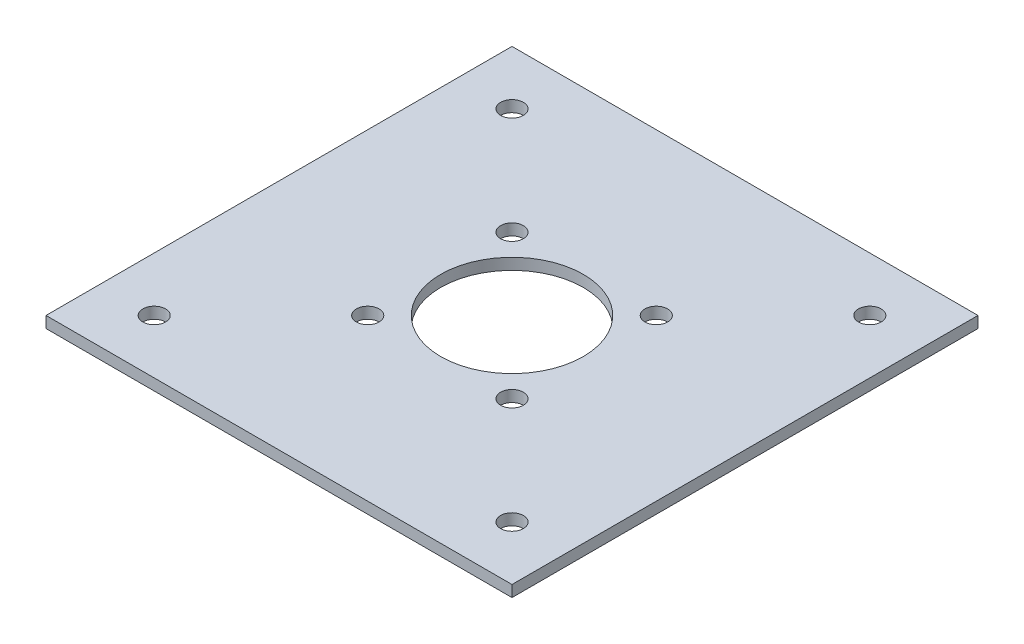
SolidWorks part; units mm, degrees
material "201 Annealed Stainless Steel (SS)"
ref_plane "Front Plane" through (0, 0, 0) normal (0, 0, 1) x (1, 0, 0)
ref_plane "Top Plane" through (0, 0, 0) normal (0, 1, 0) x (1, 0, 0)
ref_plane "Right Plane" through (0, 0, 0) normal (1, 0, 0) x (0, 0, -1)
sketch "Sketch1" plane through (0, 0, 0) normal (0, 1, 0) x (1, 0, 0)
  line L1 (0, 0) -> (82.042, 0)
  line L2 (0, 0) -> (0, 82.042)
  line L3 (0, 82.042) -> (82.042, 82.042)
  line L4 (82.042, 0) -> (82.042, 82.042)
  dimension "D1" = 82.042
  dimension "D2" = 82.042
extrude "Boss-Extrude1" add sketch "Sketch1" along normal blind 2
sketch "Sketch2" plane through (0, 2, 0) normal (0, 1, 0) x (-1, 0, 0)
  line L0 (-41.021, -82.042) -> (-41.021, 0) construction
  line L1 (-82.042, -82.042) -> (0, -82.042) construction
  line L2 (0, 0) -> (-82.042, 0) construction
  line L3 (0, -41.021) -> (-82.042, -41.021) construction
  line L4 (0, -82.042) -> (0, 0) construction
  line L5 (-82.042, 0) -> (-82.042, -82.042) construction
  line L6 (-28.321, -82.042) -> (-28.321, 0)
  line L7 (-53.721, -82.042) -> (-53.721, 0)
  line L8 (-82.042, 0) -> (-82.042, -82.042) construction
  line L9 (-72.517, 0) -> (-72.517, -82.042)
  line L10 (-9.525, 0) -> (-9.525, -82.042)
  line L11 (0, -82.042) -> (-82.042, -82.042) construction
  line L12 (0, -28.321) -> (-82.042, -28.321)
  line L13 (0, -53.721) -> (-82.042, -53.721)
  line L15 (-82.042, -9.525) -> (0, -9.525)
  line L16 (-82.042, -72.517) -> (0, -72.517)
  line L17 (-82.042, -72.517) -> (0, -72.517)
  circle A0 centre (-28.321, -53.721) radius 2
  circle A1 centre (-53.721, -53.721) radius 2
  circle A2 centre (-53.721, -28.321) radius 2
  circle A3 centre (-28.321, -28.321) radius 2
  circle A4 centre (-9.525, -9.525) radius 2
  circle A5 centre (-9.525, -72.517) radius 2
  circle A6 centre (-72.517, -9.525) radius 2
  circle A7 centre (-72.517, -72.517) radius 2
  circle A8 centre (-41.021, -41.021) radius 12.6746
  dimension "D5" = 9.525
  dimension "D1" = 12.7
  dimension "D2" = 12.7
  dimension "D3" = 12.7
  dimension "D4" = 12.7
  dimension "D6" = 9.525
extrude "Cut-Extrude1" cut sketch "Sketch2" against normal through all contours A5 | A0 | A3 | A2 | A1 | A7 | A6 | A4
sketch "Sketch3" plane through (0, 2, 0) normal (0, 1, 0) x (1, 0, 0)
  line L0 (0, 41.021) -> (82.042, 41.021) construction
  line L1 (0, 82.042) -> (0, 0) construction
  line L2 (82.042, 0) -> (82.042, 82.042) construction
  line L3 (41.021, 82.042) -> (41.021, 0) construction
  line L4 (82.042, 82.042) -> (0, 82.042) construction
  line L5 (0, 0) -> (82.042, 0) construction
  circle A0 centre (41.021, 41.021) radius 12.5476
extrude "Cut-Extrude2" cut sketch "Sketch3" against normal through all
